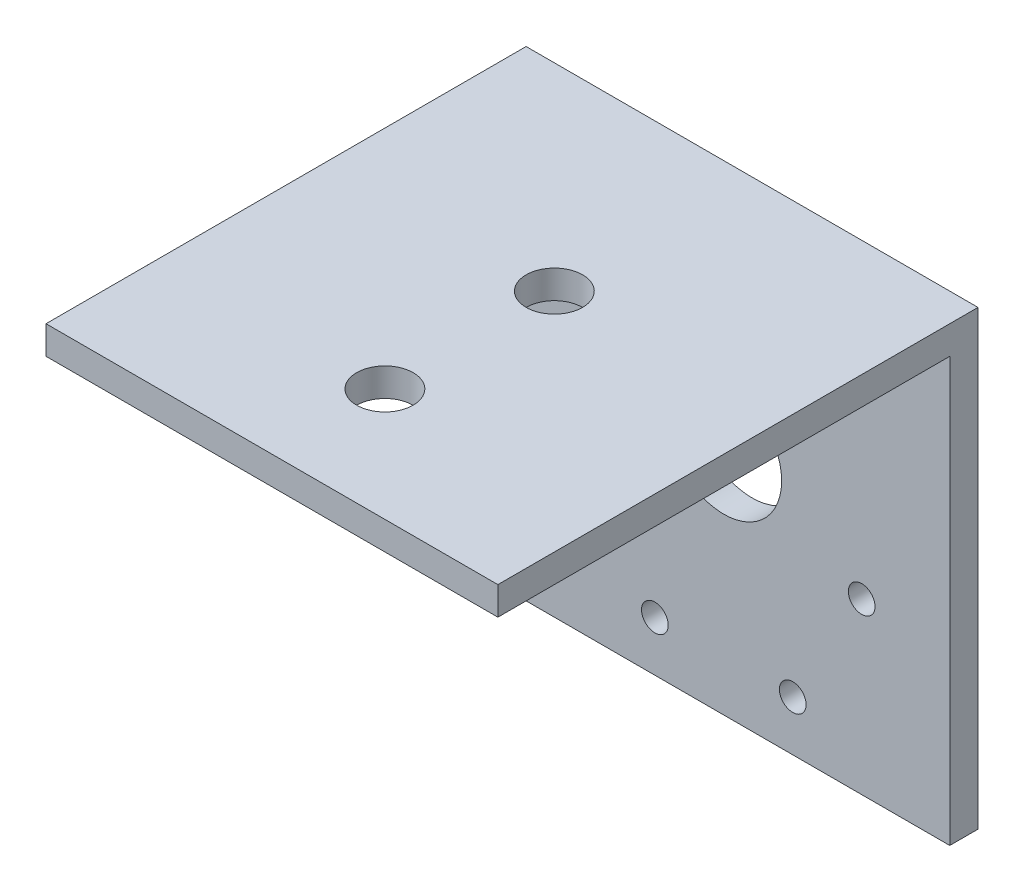
SolidWorks part; units mm, degrees
ref_plane "Front Plane" through (0, 0, 0) normal (0, 0, 1) x (1, 0, 0)
ref_plane "Top Plane" through (0, 0, 0) normal (0, 1, 0) x (1, 0, 0)
ref_plane "Right Plane" through (0, 0, 0) normal (1, 0, 0) x (0, 0, -1)
sketch "Sketch1" plane through (0, 0, 0) normal (0, 0, 1) x (1, 0, 0)
  line L0 (25.4, 50.8) -> (25.4, 0) construction
  line L1 (0, 0) -> (50.8, 0)
  line L2 (0, 0) -> (0, 50.8)
  line L3 (0, 50.8) -> (50.8, 50.8)
  line L4 (50.8, 0) -> (50.8, 50.8)
  line L6 (25.4, 19.05) -> (57.4013, 74.4779) construction
  line L7 (25.4, 19.05) -> (62.6916, -45.5409) construction
  circle A0 centre (25.4, 26.05) radius 6.5
  circle A1 centre (25.4, 19.05) radius 18.5 construction
  circle A2 centre (9.9, 19.05) radius 1.5
  circle A3 centre (40.9, 19.05) radius 1.5
  circle A4 centre (33.15, 5.6266) radius 1.5
  circle A5 centre (17.65, 5.6266) radius 1.5
  circle A6 centre (17.65, 32.4734) radius 1.5
  circle A7 centre (33.15, 32.4734) radius 1.5
  circle A8 centre (25.4, 19.05) radius 15.5 construction
  dimension "D3" = 13
  dimension "D4" = 37
  dimension "D7" = 3
  dimension "D8" = 31
  dimension "D1" = 50.8
  dimension "D2" = 50.8
  dimension "D5" = 7
  dimension "D6" = 31.75
extrude "Boss-Extrude1" add sketch "Sketch1" along normal blind 3.175
sketch "Sketch2" plane through (0, 0, 3.175) normal (0, 0, 1) x (1, 0, 0)
  line L0 (50.8, 0) -> (50.8, 50.8) construction
  line L1 (0, 50.8) -> (50.8, 50.8)
  line L2 (0, 50.8) -> (0, 47.625)
  line L3 (0, 47.625) -> (50.8, 47.625)
  line L4 (50.8, 50.8) -> (50.8, 47.625)
  dimension "D1" = 3.175
extrude "Boss-Extrude2" add sketch "Sketch2" along normal blind 50.8
sketch "Sketch3" plane through (0, 47.625, 0) normal (0, -1, 0) x (1, 0, 0)
  line L0 (25.4, 53.975) -> (25.4, 3.175) construction
  line L1 (0, 53.975) -> (50.8, 53.975) construction
  line L2 (0, 3.175) -> (50.8, 3.175) construction
  circle A0 centre (25.4, 41.275) radius 3.175
  circle A1 centre (25.4, 22.225) radius 3.175
  dimension "D1" = 6.35
  dimension "D2" = 19.05
  dimension "D3" = 12.7
extrude "Cut-Extrude1" cut sketch "Sketch3" against normal through all
